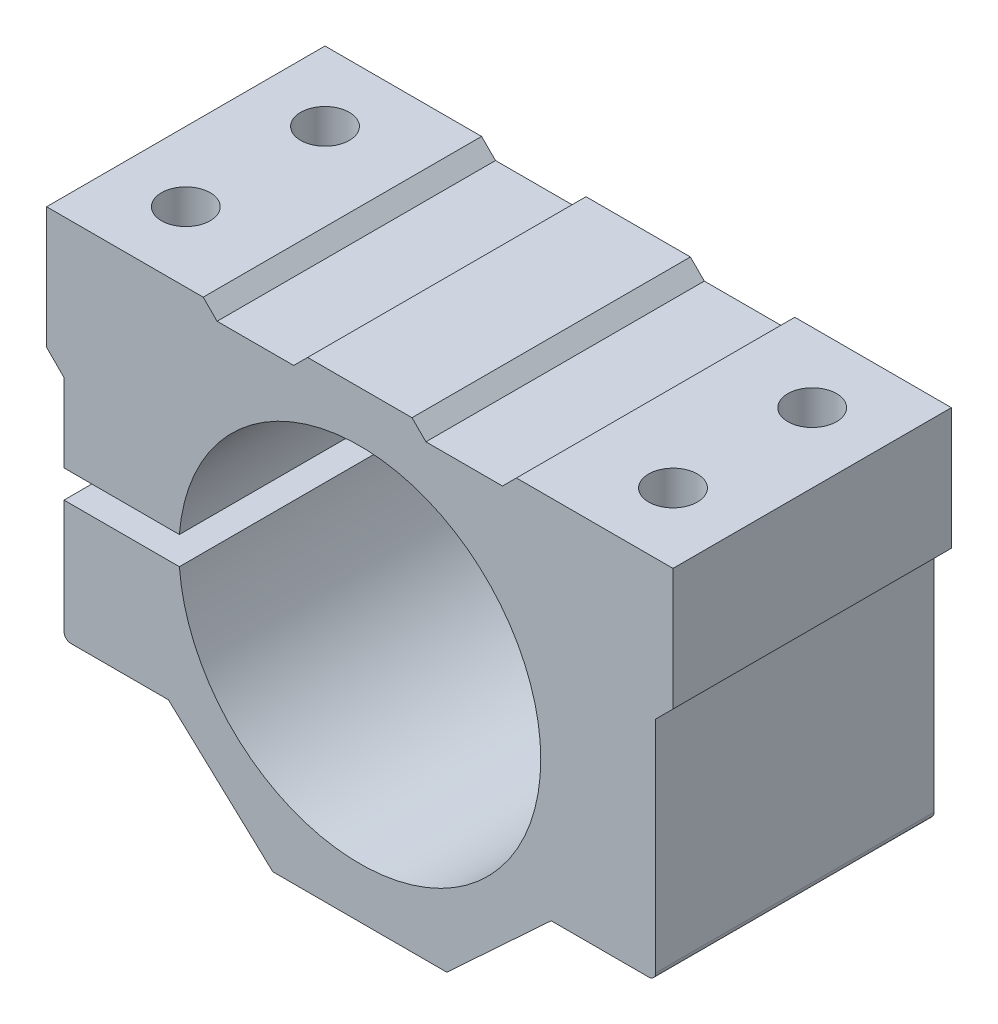
SolidWorks part; units mm, degrees
material "6061 合金"
ref_plane "前视基准面" through (0, 0, 0) normal (0, 0, 1) x (1, 0, 0)
ref_plane "上视基准面" through (0, 0, 0) normal (0, 1, 0) x (1, 0, 0)
ref_plane "右视基准面" through (0, 0, 0) normal (1, 0, 0) x (0, 0, -1)
sketch "草图1" plane through (0, 0, 0) normal (0, 0, 1) x (1, 0, 0)
  line L0 (0, -571.0615) -> (0, 27982.0142) construction
  line L1 (-12.5, -33.25) -> (12.5, -33.25)
  line L2 (-45, 33.25) -> (-45, 15.75)
  line L3 (-45, 15.75) -> (-42.5, 13.25)
  line L4 (-42.5, 13.25) -> (-42.5, -19.35)
  line L5 (27.5, -19.35) -> (12.5, -33.25)
  line L6 (-27.5, -19.35) -> (-12.5, -33.25)
  line L7 (-20.5, 31.25) -> (-9.5, 31.25)
  line L8 (-42.5, -19.35) -> (-27.5, -19.35)
  line L9 (-9.5, 31.25) -> (-7.5, 33.25)
  line L10 (-7.5, 33.25) -> (7.5, 33.25)
  line L11 (42.5, -19.35) -> (27.5, -19.35)
  line L12 (42.5, 13.25) -> (42.5, -19.35)
  line L13 (45, 15.75) -> (42.5, 13.25)
  line L14 (45, 33.25) -> (45, 15.75)
  line L15 (-45, 33.25) -> (-22.5, 33.25)
  line L16 (-22.5, 33.25) -> (-20.5, 31.25)
  line L17 (45, 33.25) -> (22.5, 33.25)
  line L18 (22.5, 33.25) -> (20.5, 31.25)
  line L19 (20.5, 31.25) -> (9.5, 31.25)
  line L20 (9.5, 31.25) -> (7.5, 33.25)
  circle A0 centre (0, 0) radius 26
  point P7 (-42.5, -19.35)
  point P22 (0, -33.25)
  point P33 (0, 33.25)
  dimension "D9" = 52
  dimension "D2" = 45
  dimension "D3" = 12.5
  dimension "D4" = 2.5
  dimension "D5" = 27.5
  dimension "D6" = 52.6
  dimension "D7" = 20
  dimension "D8" = 7.5
  dimension "D11" = 2
  dimension "D13" = 45
  dimension "D10" = 66.5
  dimension "D12" = 22.5
  dimension "D14" = 17.5
  dimension "D15" = 33.25
extrude "凸台-拉伸1" add sketch "草图1" along normal blind 40
sketch "草图2" plane through (0, 33.25, 0) normal (0, 1, 0) x (1, 0, 0)
  line L0 (0, -1036) -> (0, 48964) construction
  line L2 (-1021, -20) -> (48979, -20) construction
  line L3 (-45, -40) -> (-45, 0) construction
  line L4 (7.5, -40) -> (-7.5, -40) construction
  circle A0 centre (-35, -10) radius 3.5
  circle A1 centre (-35, -30) radius 3.5
  circle A2 centre (35, -30) radius 3.5
  circle A3 centre (35, -10) radius 3.5
  point P5 (0, -40)
  point P10 (-45, -20)
  dimension "D1" = 7
  dimension "D2" = 35
  dimension "D3" = 10
extrude "切除-拉伸1" cut sketch "草图2" against normal through all
sketch "草图3" plane through (0, 0, 0) normal (0, 0, 1) x (1, 0, 0)
  line L0 (-1000, 0) -> (49000, 0) construction
  line L2 (-48.6147, 2) -> (-14.9548, 2)
  line L3 (-48.6147, 2) -> (-48.6147, -2)
  line L4 (-48.6147, -2) -> (-14.9548, -2)
  line L5 (-14.9548, 2) -> (-14.9548, -2)
  line L6 (-48.6147, 2) -> (-14.9548, -2) construction
  line L7 (-48.6147, -2) -> (-14.9548, 2) construction
  point P7 (-31.7847, 0)
  dimension "D1" = 4
extrude "切除-拉伸3" cut sketch "草图3" along normal through all
fillet "圆角1" radius 1 2 edges at (42.5, -19.35, 20) (-42.5, -19.35, 20)
